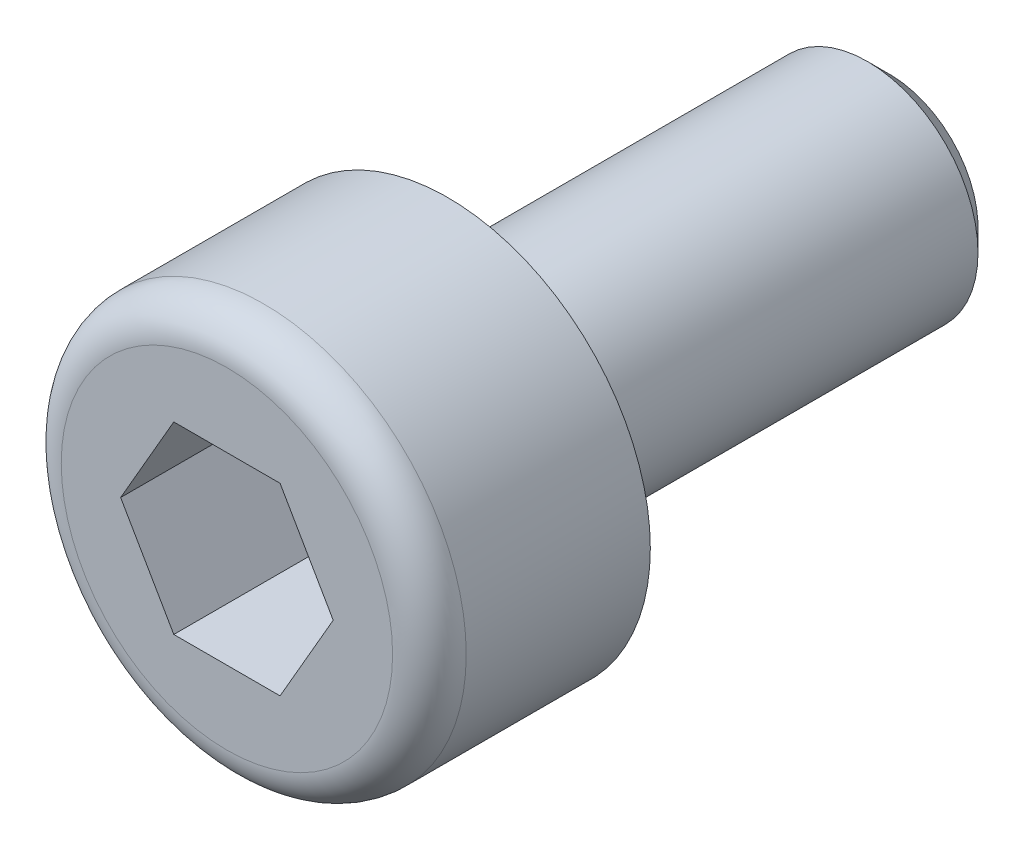
SolidWorks part; units mm, degrees
material "Ocel prostá uhlíková"
ref_plane "Přední rovina" through (0, 0, 0) normal (0, 0, 1) x (1, 0, 0)
ref_plane "Horní rovina" through (0, 0, 0) normal (0, 1, 0) x (1, 0, 0)
ref_plane "Pravá rovina" through (0, 0, 0) normal (1, 0, 0) x (0, 0, -1)
sketch "Skica1" plane through (0, 0, 0) normal (0, 0, 1) x (1, 0, 0)
  line L0 (0, 0) -> (-5.7735, 0) construction
  circle A0 centre (0, 0) radius 2.75
  dimension "D1" = 5.5
extrude "Přidat vysunutím1" add sketch "Skica1" along normal blind 3
sketch "Skica4" plane through (0, 0, 3) normal (0, 0, 1) x (1, 0, 0)
  line L1 (-1.4434, 0) -> (-0.7217, -1.25)
  line L2 (-0.7217, -1.25) -> (0.7217, -1.25)
  line L3 (0.7217, -1.25) -> (1.4434, 0)
  line L4 (1.4434, 0) -> (0.7217, 1.25)
  line L5 (0.7217, 1.25) -> (-0.7217, 1.25)
  line L6 (-0.7217, 1.25) -> (-1.4434, 0)
  line L7 (0, 0) -> (-5.7735, 0) construction
  circle A0 centre (0, 0) radius 1.25 construction
  dimension "D1" = 2.5
extrude "Odebrat vysunutím1" cut sketch "Skica4" against normal blind 2
sketch "Skica2" plane through (0, 0, 0) normal (0, 0, -1) x (-1, 0, 0)
  circle A0 centre (0, 0) radius 1.5
  dimension "D1" = 3
extrude "Přidat vysunutím2" add sketch "Skica2" along normal blind 6
chamfer "Zkosení1" distance 0.3 angle 45 1 edges at (-1.5, 0, -6)
fillet "Zaoblit1" radius 0.5 1 edges at (2.75, 0, 3)
